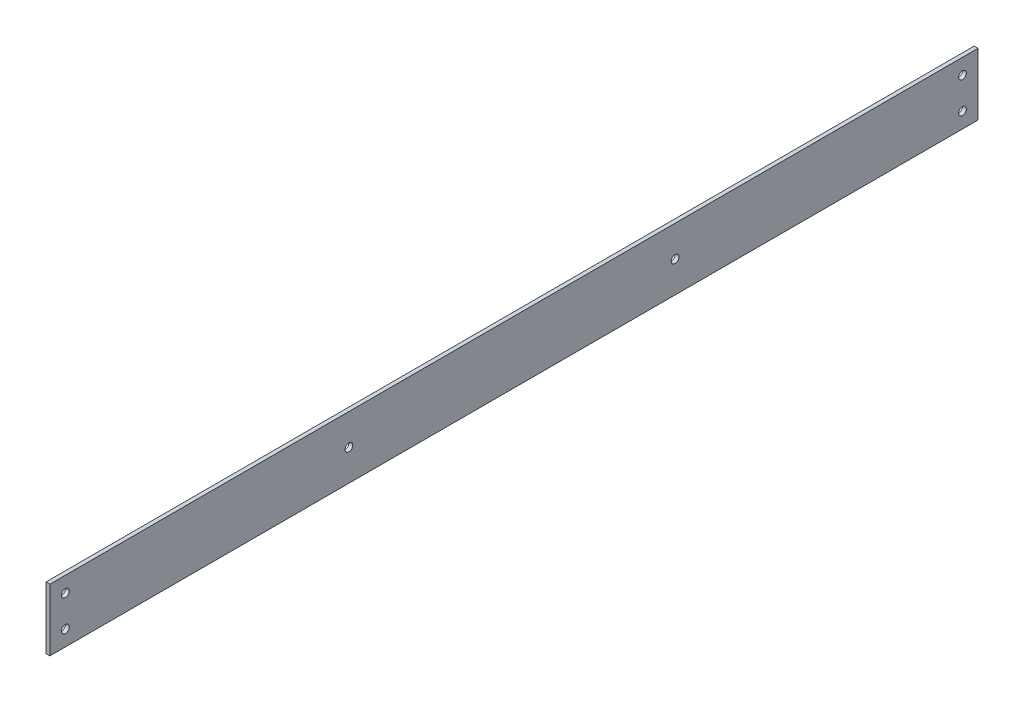
SolidWorks part; units mm, degrees
ref_plane "Front Plane" through (0, 0, 0) normal (0, 0, 1) x (1, 0, 0)
ref_plane "Top Plane" through (0, 0, 0) normal (0, 1, 0) x (1, 0, 0)
ref_plane "Right Plane" through (0, 0, 0) normal (1, 0, 0) x (0, 0, -1)
sketch "Sketch1" plane through (0, 0, 0) normal (0, 0, 1) x (1, 0, 0)
  line L1 (-1.5875, -25.4) -> (1.5875, -25.4)
  line L2 (-1.5875, -25.4) -> (-1.5875, 25.4)
  line L3 (-1.5875, 25.4) -> (1.5875, 25.4)
  line L4 (1.5875, -25.4) -> (1.5875, 25.4)
  line L5 (-1.5875, -25.4) -> (1.5875, 25.4) construction
  line L6 (-1.5875, 25.4) -> (1.5875, -25.4) construction
  point P0 (0, 0)
  dimension "D1" = 50.8
  dimension "D2" = 3.175
extrude "Boss-Extrude1" add sketch "Sketch1" along normal blind 809.625
sketch "Sketch2" plane through (1.5875, 0, 0) normal (1, 0, 0) x (0, 0, -1)
  line L0 (0, -25.4) -> (0, 25.4) construction
  line L1 (-809.625, 25.4) -> (0, 25.4) construction
  line L3 (-809.625, -25.4) -> (0, -25.4) construction
  line L4 (-404.8125, -25.4) -> (-404.8125, 25.4) construction
  line L5 (-809.625, -25.4) -> (0, -25.4) construction
  circle A0 centre (-38.1, 12.7) radius 3.175
  circle A1 centre (-38.1, -12.7) radius 3.175
  circle A2 centre (-771.525, 12.7) radius 3.175
  circle A3 centre (-771.525, -12.7) radius 3.175
  dimension "D3" = 6.35
  dimension "D6" = 6.35
  dimension "D1" = 38.1
  dimension "D2" = 12.7
  dimension "D4" = 38.1
  dimension "D5" = 12.7
extrude "Cut-Extrude1" cut sketch "Sketch2" against normal through all
sketch "Sketch3" plane through (-1.5875, 0, 0) normal (-1, 0, 0) x (0, 0, 1)
  line L0 (809.625, 25.4) -> (0, 25.4) construction
  line L1 (809.625, -25.4) -> (784.225, -25.4)
  line L2 (809.625, -25.4) -> (809.625, 25.4)
  line L3 (809.625, 25.4) -> (784.225, 25.4)
  line L4 (784.225, -25.4) -> (784.225, 25.4)
  line L5 (809.625, -25.4) -> (0, -25.4) construction
  line L6 (0, -25.4) -> (25.4, -25.4)
  line L7 (0, -25.4) -> (0, 25.4)
  line L8 (0, 25.4) -> (25.4, 25.4)
  line L9 (25.4, -25.4) -> (25.4, 25.4)
  line L10 (0, 25.4) -> (0, -25.4) construction
  point P13 (0, 25.4)
  dimension "D1" = 25.4
extrude "Cut-Extrude2" cut sketch "Sketch3" against normal through all
sketch "Sketch4" plane through (-1.5875, 0, 0) normal (-1, 0, 0) x (0, 0, 1)
  line L0 (784.225, -25.4) -> (25.4, -25.4) construction
  line L1 (25.4, -25.4) -> (25.4, 25.4) construction
  circle A2 centre (273.05, 0) radius 3.175
  circle A3 centre (539.75, 0) radius 3.175
  point P8 (0, 0)
  point P9 (0, 0)
  dimension "D1" = 6.35
  dimension "D2" = 25.4
  dimension "D3" = 266.7
  dimension "D4" = 247.65
extrude "Cut-Extrude3" cut sketch "Sketch4" against normal through all
